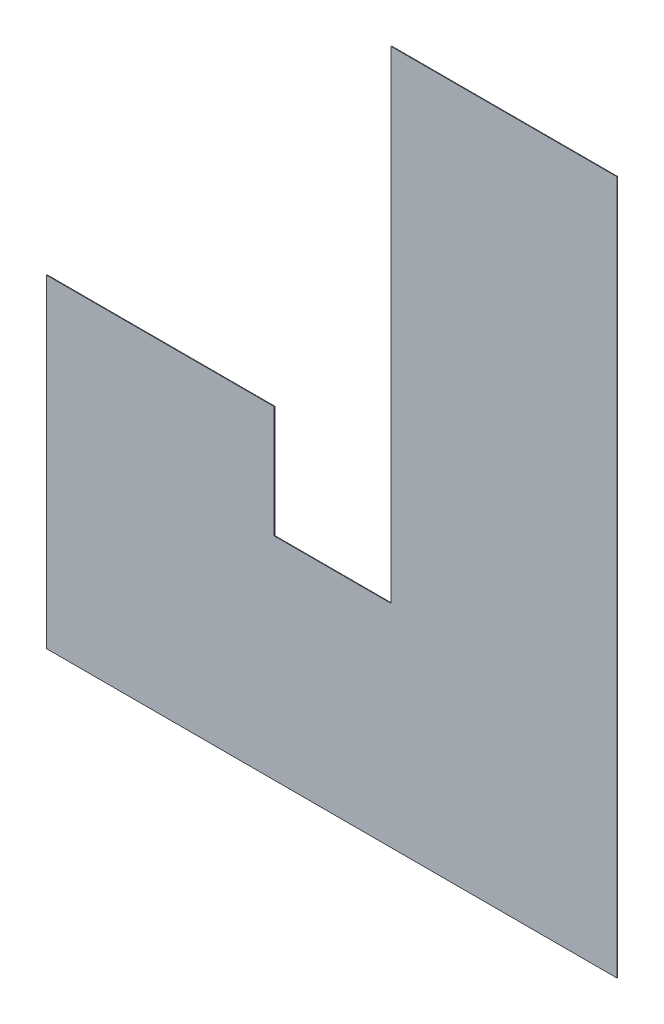
SolidWorks part; units mm, degrees
ref_plane "Plano frontal" through (0, 0, 0) normal (0, 0, 1) x (1, 0, 0)
ref_plane "Plano superior" through (0, 0, 0) normal (0, 1, 0) x (1, 0, 0)
ref_plane "Plano direito" through (0, 0, 0) normal (1, 0, 0) x (0, 0, -1)
sketch "Sketch1" plane through (0, 0, 43822.9795) normal (0, 0, 1) x (1, 0, 0)
  line L0 (-14521.6177, -20082.5186) -> (-42361.227, -20082.5186) construction
  line L1 (-7996.6177, 3307.4814) -> (-15606.6177, 3307.4814)
  line L2 (-7996.6177, 3307.4814) -> (-7996.6177, -20082.5186)
  line L3 (-7996.6177, -20082.5186) -> (-15606.6177, -20082.5186)
  line L4 (-15606.6177, 3307.4814) -> (-15606.6177, -20082.5186)
  line L5 (-16246.6177, -12952.1146) -> (-19546.6177, -12952.1146) construction
  line L6 (-15606.6177, -20082.5186) -> (-27221.6177, -20082.5186)
  line L7 (-15606.6177, -20082.5186) -> (-15606.6177, -12952.1146)
  line L8 (-15606.6177, -12952.1146) -> (-27221.6177, -12952.1146)
  line L9 (-27221.6177, -20082.5186) -> (-27221.6177, -12952.1146)
  line L10 (-27221.6177, -17042.5186) -> (-27221.6177, -9082.5186) construction
  line L12 (-27221.6177, -12952.1146) -> (-19546.6177, -12952.1146)
  line L13 (-27221.6177, -12952.1146) -> (-27221.6177, -9177.1146)
  line L14 (-27221.6177, -9177.1146) -> (-19546.6177, -9177.1146)
  line L15 (-19546.6177, -12952.1146) -> (-19546.6177, -9177.1146)
  point P4 (0, 0)
  line M2 (-19546.6177, -9107.5186) -> (-19546.6177, -12882.5186)
extrude "Boss-Extrude1" add sketch "Sketch1" along normal blind 20 contours L1 L4 L3 L2 | L9 L6 L4 L8 | L8 L15 L14 L13 M2
